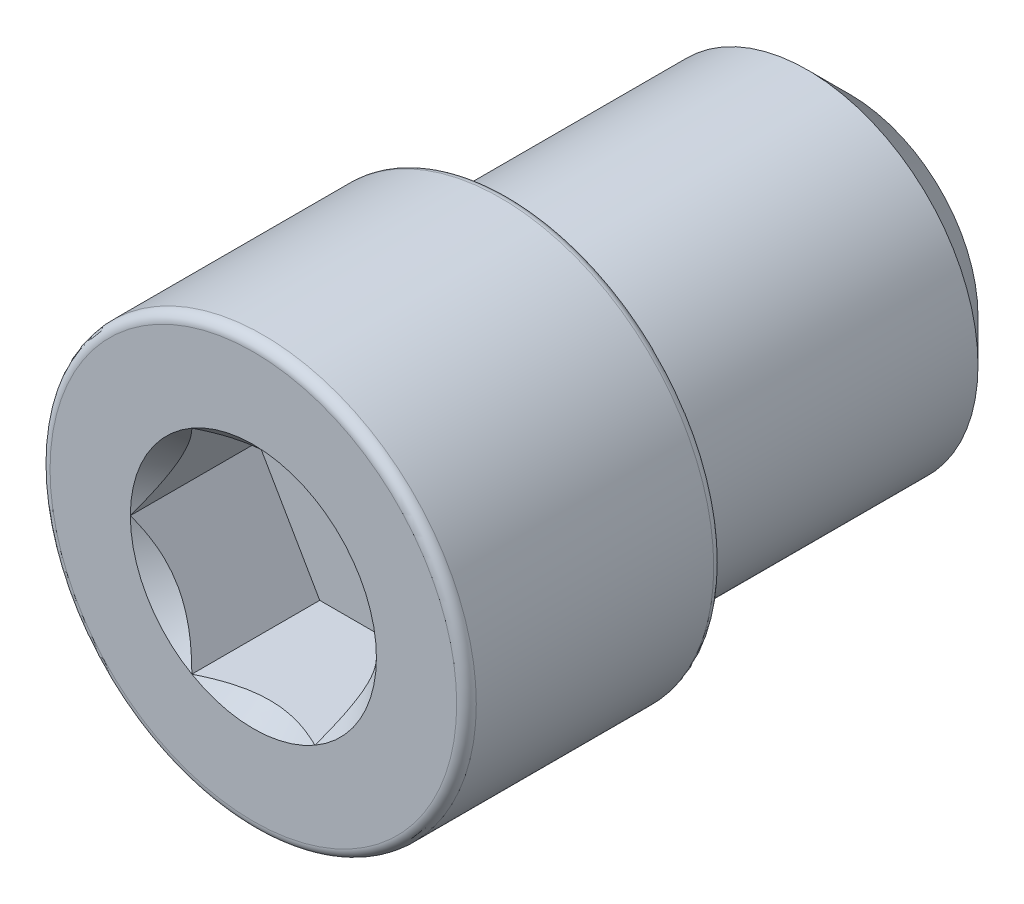
SolidWorks part; units mm, degrees
material "Acciaio inossidabile (ferroso)"
ref_plane "Piano frontale" through (0, 0, 0) normal (0, 0, 1) x (1, 0, 0)
ref_plane "Piano superiore" through (0, 0, 0) normal (0, 1, 0) x (1, 0, 0)
ref_plane "Piano destro" through (0, 0, 0) normal (1, 0, 0) x (0, 0, -1)
sketch "Schizzo1" plane through (0, 0, 0) normal (0, 0, 1) x (1, 0, 0)
  circle A0 centre (0, 0) radius 4
  dimension "D1" = 8
extrude "Estrusione-Estrusione1" add sketch "Schizzo1" along normal blind 8
cosmetic thread "Filettatura cosmetica2" parameters "D2"=6.619
chamfer "Smusso1" distance 1 angle 45 1 edges at (4, 0, 0)
sketch "Schizzo6" plane through (0, 0, 8) normal (0, 0, 1) x (1, 0, 0)
  circle A0 centre (0, 0) radius 5
  dimension "D1" = 10
extrude "Estrusione-Estrusione3" add sketch "Schizzo6" along normal blind 6
sketch "Schizzo7" plane through (0, 0, 14) normal (0, 0, 1) x (1, 0, 0)
  line L1 (1.4434, 2.5) -> (-1.4434, 2.5)
  line L2 (-1.4434, 2.5) -> (-2.8868, 0)
  line L3 (-2.8868, 0) -> (-1.4434, -2.5)
  line L4 (-1.4434, -2.5) -> (1.4434, -2.5)
  line L5 (1.4434, -2.5) -> (2.8868, 0)
  line L6 (2.8868, 0) -> (1.4434, 2.5)
  circle A1 centre (0, 0) radius 2.5 construction
  dimension "D1" = 5
extrude "Taglio-Estrusione3" cut sketch "Schizzo7" against normal blind 3
sketch "Schizzo8" plane through (0, 0, 14) normal (0, 0, 1) x (1, 0, 0)
  circle A0 centre (0, 0) radius 2.8868
extrude "Taglio-Estrusione4" cut sketch "Schizzo8" against normal blind 1 draft 45
fillet "Raccordo1" radius 0.23 1 edges at (5, 0, 14)
fillet "Raccordo2" radius 0.2 1 edges at (5, 0, 8)
